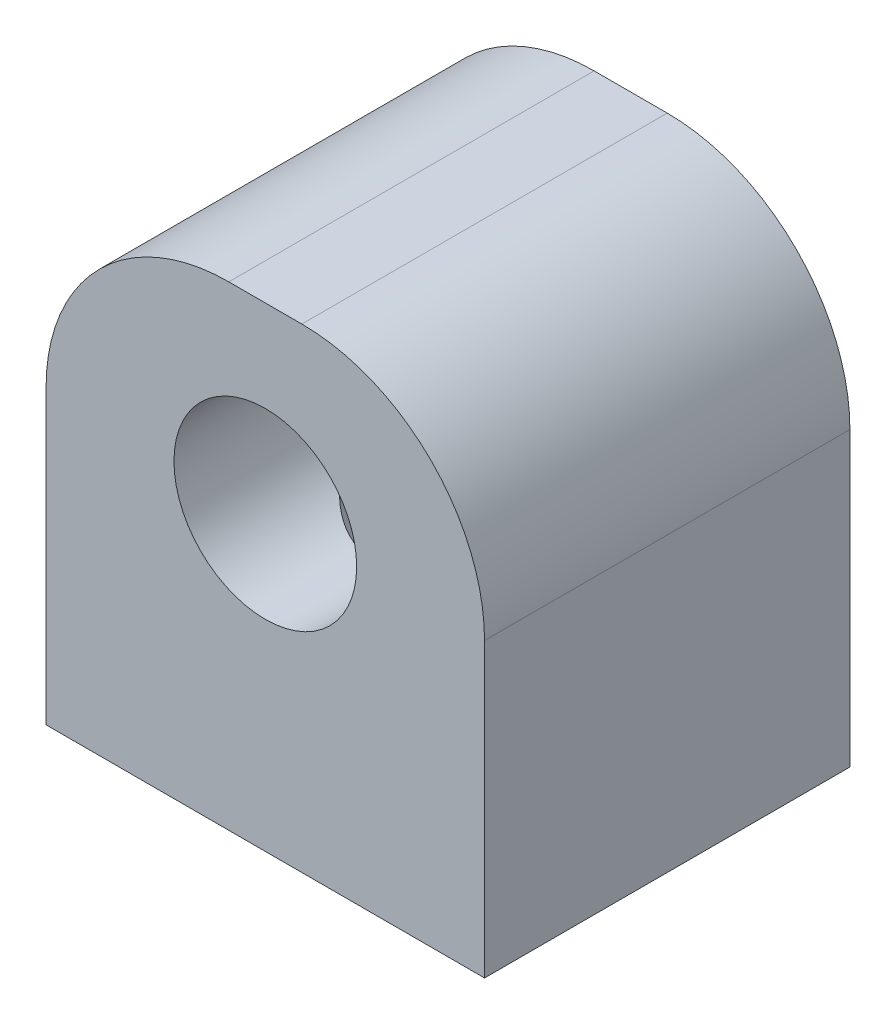
SolidWorks part; units mm, degrees
ref_plane "Plan de face" through (0, 0, 0) normal (0, 0, 1) x (1, 0, 0)
ref_plane "Plan de dessus" through (0, 0, 0) normal (0, 1, 0) x (1, 0, 0)
ref_plane "Plan de droite" through (0, 0, 0) normal (1, 0, 0) x (0, 0, -1)
ref_plane "Plan1" through (0, 0, 0) normal (0, 0, -1) x (-1, 0, 0)
sketch "Esquisse1" plane through (0, 0, 0) normal (0, 0, -1) x (-1, 0, 0)
  line L0 (6, -8) -> (6, 5)
  line L1 (6, 5) -> (-6, 5)
  line L2 (-6, 5) -> (-6, -8)
  line L3 (-6, -8) -> (6, -8)
extrude "Boss.-Extru.1" add sketch "Esquisse1" against normal blind 10
sketch "Esquisse3" plane through (0, 0, 0) normal (0, 1, 0) x (1, 0, 0)
  line L0 (2.5, 0) -> (0, 0)
  line L1 (0, 0) -> (0, -10)
  line L2 (0, -10) -> (2.5, -10)
  line L3 (2.5, -10) -> (2.5, 0)
  line L4 (0, 0) -> (0, -10) construction
  dimension "D1" = 2.5
revolve "Enlèvement de matière-Révolution1" cut sketch "Esquisse3" angle 360 about L4
ref_plane "Plan2" through (0, 0, 0) normal (0, 1, 0) x (1, 0, 0)
hole_wizard "Diamètre du perçage Ø5.6 (5.6)1" positions "Esquisse5" profile "Esquisse4" hole size "Ø5.6" standard "Ansi Metric"
sketch "Esquisse5" plane through (0, 0, 0) normal (0, 1, 0) x (1, 0, 0)
  point P0 (0, -5)
sketch "Esquisse4" plane through (0, 0, 5) normal (1, 0, 0) x (0, 0, 1)
  line L0 (0, 0) -> (0, 8)
  line L1 (0, 8) -> (2.1, 8)
  line L2 (2.1, 8) -> (2.1, 0)
  line L5 (2.1, 0) -> (0, 0)
  line L11 (0, -6.35) -> (0, 107.95) construction
  dimension "Diamètre du perçage jusqu'au prochain" = 4.2
  dimension "Profondeur du perçage jusqu'au prochain" = 8
fillet "Congé1" radius 5 2 edges at (-6, 5, 5) (6, 5, 5)
